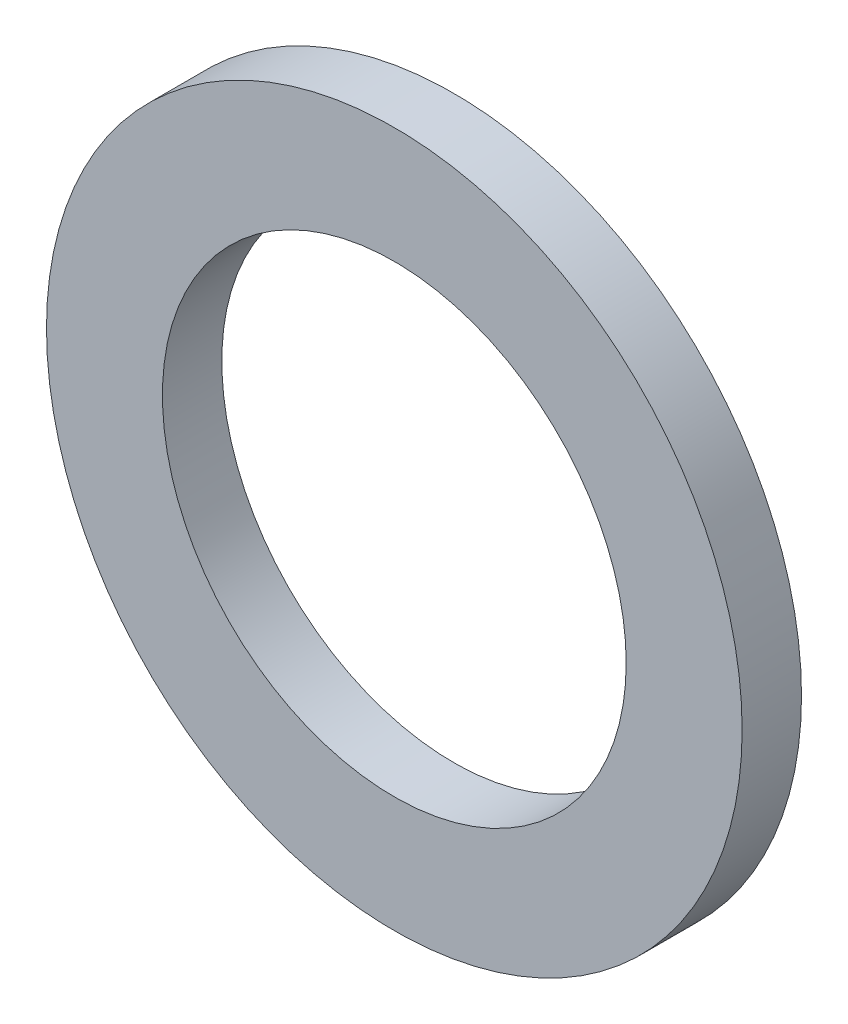
SolidWorks part; units mm, degrees
ref_plane "Front Plane" through (0, 0, 0) normal (0, 0, 1) x (1, 0, 0)
ref_plane "Top Plane" through (0, 0, 0) normal (0, 1, 0) x (1, 0, 0)
ref_plane "Right Plane" through (0, 0, 0) normal (1, 0, 0) x (0, 0, -1)
sketch "Sketch1" plane through (0, 0, 0) normal (0, 1, 0) x (1, 0, 0)
  line L0 (1.5875, -0.4064) -> (2.3812, -0.4064)
  line L1 (2.3812, -0.4064) -> (2.3812, 0)
  line L2 (2.3812, 0) -> (1.5875, 0)
  line L3 (1.5875, 0) -> (1.5875, -0.4064)
  line L4 (0, 0) -> (0, -0.4064) construction
revolve "Revolve1" add sketch "Sketch1" angle 360 about L4
